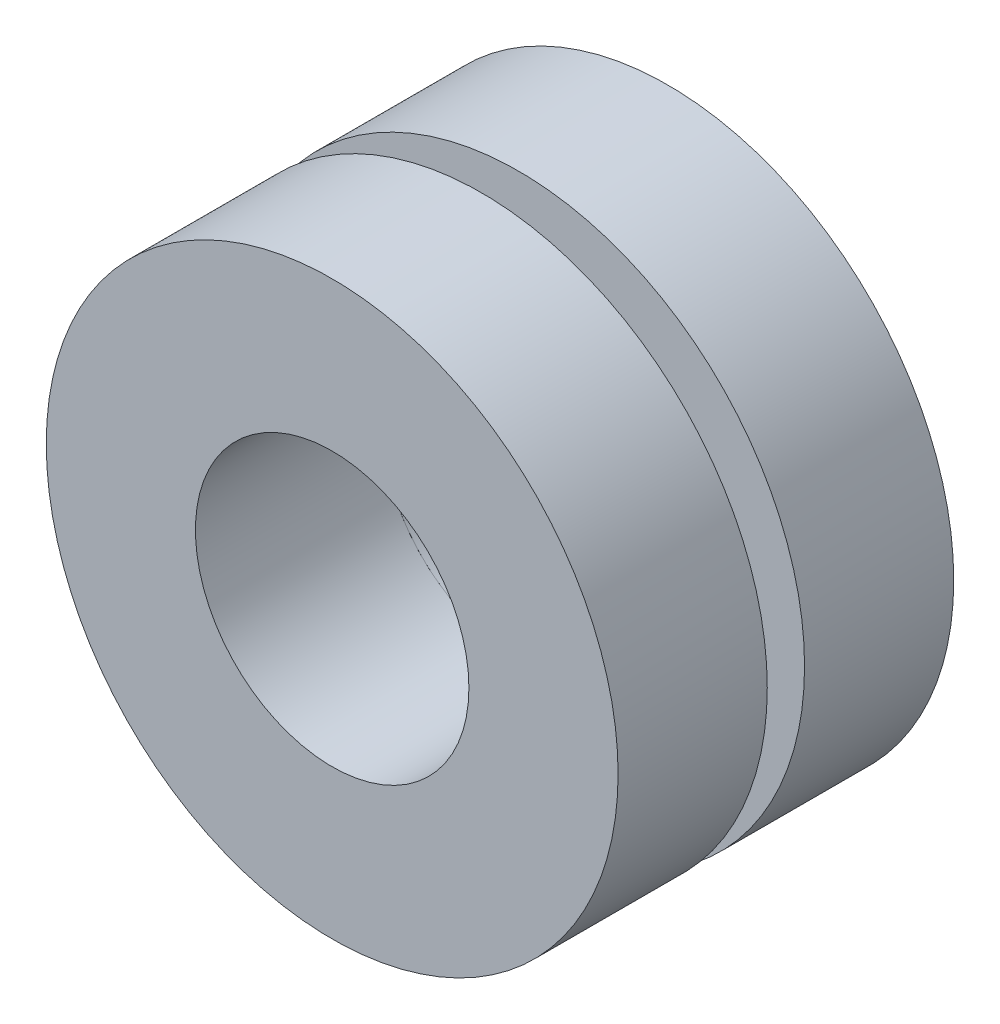
SolidWorks part; units mm, degrees
ref_plane "Front Plane" through (0, 0, 0) normal (0, 0, 1) x (1, 0, 0)
ref_plane "Top Plane" through (0, 0, 0) normal (0, 1, 0) x (1, 0, 0)
ref_plane "Right Plane" through (0, 0, 0) normal (1, 0, 0) x (0, 0, -1)
sketch "Sketch1" plane through (0, 0, 0) normal (0, 0, 1) x (1, 0, 0)
  circle A0 centre (0, 0) radius 2.794
  circle A1 centre (0, 0) radius 4.572
  dimension "D1" = 1.778
  dimension "D2" = 5.588
extrude "Boss-Extrude2" add sketch "Sketch1" along normal blind 0.762 contours A1
sketch "Sketch3" plane through (0, 0, 0.762) normal (0, 0, 1) x (1, 0, 0)
  circle A0 centre (0, 0) radius 2.794
  circle A1 centre (0, 0) radius 5.842
  dimension "D1" = 3.048
  dimension "D2" = 5.588
extrude "Boss-Extrude3" add sketch "Sketch3" along normal blind 3.048
sketch "Sketch4" plane through (0, 0, 0) normal (0, 0, -1) x (-1, 0, 0)
  circle A0 centre (0, 0) radius 2.794
  circle A1 centre (0, 0) radius 5.842
  dimension "D1" = 5.588
  dimension "D2" = 11.684
extrude "Boss-Extrude4" add sketch "Sketch4" along normal blind 3.048 separate body
